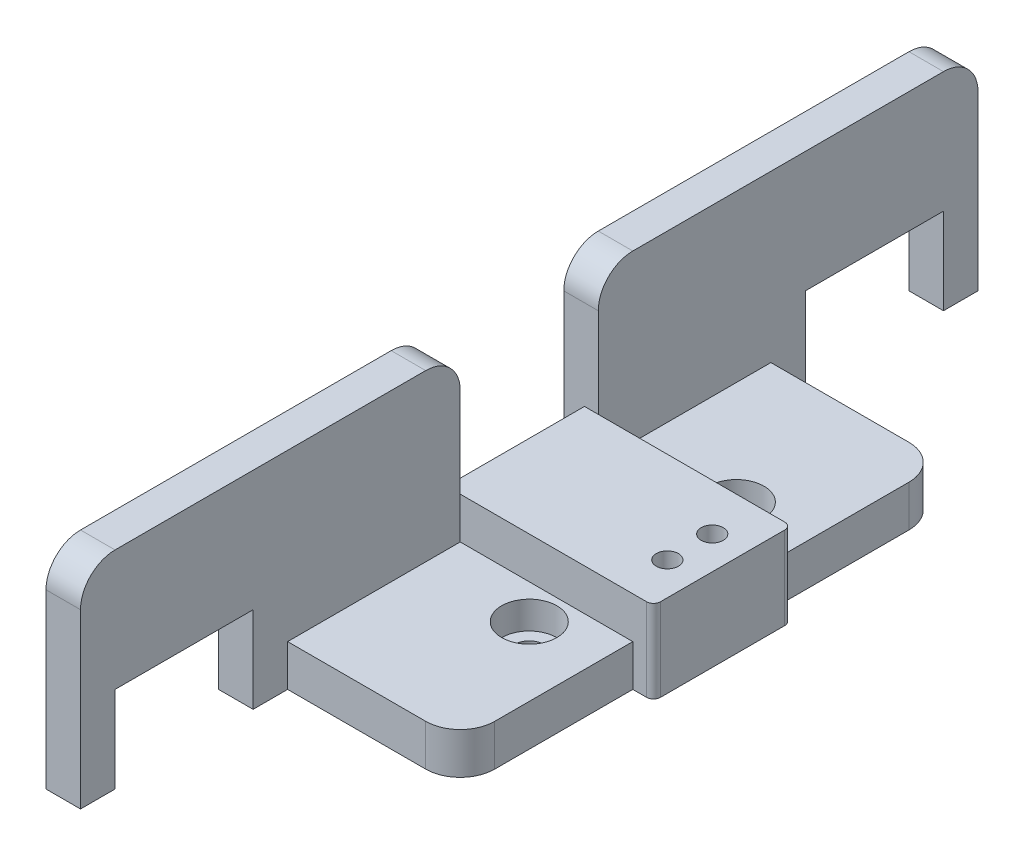
SolidWorks part; units mm, degrees
ref_plane "Front Plane" through (0, 0, 0) normal (0, 0, 1) x (1, 0, 0)
ref_plane "Top Plane" through (0, 0, 0) normal (0, 1, 0) x (1, 0, 0)
ref_plane "Right Plane" through (0, 0, 0) normal (1, 0, 0) x (0, 0, -1)
sketch "Sketch1" plane through (0, 0, 0) normal (0, 1, 0) x (1, 0, 0)
  line L0 (-25, -35) -> (-25, -65)
  line L1 (-25, 35) -> (0, 35)
  line L3 (-25, -35) -> (0, -35)
  line L4 (0, 35) -> (0, -35)
  line L5 (-30, 65) -> (-25, 65)
  line L6 (-30, 65) -> (-30, -65)
  line L7 (-30, -65) -> (-25, -65)
  line L8 (-25, 65) -> (-25, 35)
  point P4 (0, 0)
  point P10 (-30, 0)
  dimension "D1" = 30
  dimension "D2" = 70
  dimension "D3" = 130
  dimension "D4" = 5
extrude "Boss-Extrude1" add sketch "Sketch1" along normal blind 6
sketch "Sketch2" plane through (0, 6, 0) normal (0, 1, 0) x (1, 0, 0)
  line L1 (-30, 65) -> (-25, 65)
  line L2 (-30, 65) -> (-30, -65)
  line L3 (-30, -65) -> (-25, -65)
  line L4 (-25, 65) -> (-25, -65)
extrude "Boss-Extrude2" add sketch "Sketch2" along normal blind 24
sketch "Sketch3" plane through (-30, 0, 0) normal (-1, 0, 0) x (0, 0, 1)
  line L0 (0, 0) -> (0, 30) construction
  line L1 (-65, 30) -> (65, 30) construction
  line L2 (-65, 0) -> (65, 0) construction
  line L3 (-60, 0) -> (-40, 0)
  line L4 (-60, 0) -> (-60, 12.5)
  line L5 (-60, 12.5) -> (-40, 12.5)
  line L6 (-40, 0) -> (-40, 12.5)
  line L7 (60, 12.5) -> (40, 12.5)
  line L8 (40, 0) -> (40, 12.5)
  line L9 (60, 0) -> (40, 0)
  line L10 (60, 0) -> (60, 12.5)
  point P15 (-50, 0)
  point P16 (50, 0)
  dimension "D1" = 100
  dimension "D2" = 20
  dimension "D3" = 12.5
extrude "Cut-Extrude1" cut sketch "Sketch3" against normal through all
sketch "Sketch4" plane through (0, 6, 0) normal (0, 1, 0) x (1, 0, 0)
  line L0 (0, 0) -> (-30, 0) construction
  line L1 (-30, 65) -> (-30, -65) construction
  line L2 (-10, 35) -> (-10, -35) construction
  line L3 (0, 35) -> (-25, 35) construction
  line L4 (-25, -35) -> (0, -35) construction
  line L5 (-25, -35) -> (-25, 35) construction
  line L6 (0, 30) -> (-25, 30) construction
  line L7 (0, 30) -> (0, -30) construction
  line L8 (0, -30) -> (-25, -30) construction
  line L9 (-25, 30) -> (-25, -30) construction
  point P5 (-10, 0)
  point P16 (0, 0)
  point P17 (-10, 15)
  point P18 (-10, -15)
  dimension "D1" = 20
  dimension "D2" = 60
  dimension "D3" = 30
hole_wizard "CBORE for M4 SHCS1" positions "Sketch8" profile "Sketch6" counterbore size "M4" standard "ANSI Metric" end condition through all
sketch "Sketch8" plane through (0, 6, 0) normal (0, 1, 0) x (1, 0, 0)
  point P4 (-10, 15)
  point P7 (-10, -15)
sketch "Sketch6" plane through (-10, 6, -15) normal (1, 0, 0) x (0, 0, 1)
  line L0 (0, 0) -> (0, 6)
  line L1 (0, 6) -> (2.25, 6)
  line L3 (2.25, 6) -> (2.25, 4)
  line L4 (2.25, 4) -> (4, 4)
  line L5 (4, 4) -> (4, 0)
  line L7 (4, 0) -> (0, 0)
  line L11 (0, -6.35) -> (0, 107.95) construction
  dimension "Thru Hole Dia." = 4.5
  dimension "Thru Hole Depth" = 6
  dimension "C'Bore Dia." = 8
  dimension "C'Bore Depth" = 4
sketch "Sketch9" plane through (0, 30, 0) normal (0, 1, 0) x (1, 0, 0)
  line L0 (-30, 65) -> (-30, -65) construction
  line L1 (-30, 10) -> (-25, 10)
  line L2 (-30, 10) -> (-30, -10)
  line L3 (-30, -10) -> (-25, -10)
  line L4 (-25, 10) -> (-25, -10)
  line L5 (-25, 30) -> (-25, -30) construction
  point P8 (-30, 0)
  dimension "D1" = 20
extrude "Cut-Extrude2" cut sketch "Sketch9" against normal blind 18
sketch "Sketch10" plane through (0, 12, 0) normal (0, 1, 0) x (1, 0, 0)
  line L0 (-30, -10) -> (-25, -10) construction
  line L1 (-30, 10) -> (3, 10)
  line L2 (-30, 10) -> (-30, -10)
  line L3 (-30, -10) -> (3, -10)
  line L4 (3, 10) -> (3, -10)
  dimension "D1" = 33
extrude "Boss-Extrude3" add sketch "Sketch10" against normal through all
sketch "Sketch11" plane through (0, 12, 0) normal (0, 1, 0) x (1, 0, 0)
  line L0 (-1.75, 4.5339) -> (-1.75, -4.5339) construction
  line L2 (0, 0) -> (-42.0241, 0) construction
  line L3 (3, -10) -> (3, 10) construction
  circle A0 centre (-1.75, 3.25) radius 1.6
  circle A1 centre (-1.75, -3.25) radius 1.6
  point P2 (-1.75, 0)
  point P8 (-1.75, 3.25)
  point P9 (-1.75, -3.25)
  dimension "D3" = 3.2
  dimension "D1" = 4.75
  dimension "D2" = 6.5
fillet "Fillet1" radius 5 6 edges at (-27.5, 30, -65) (0, 3, -35) (0, 3, 35) (-27.5, 30, 65) (-27.5, 30, -10) (-27.5, 30, 10)
fillet "Fillet2" [suppressed] radius 2
sketch "Sketch13" plane through (-30, 0, 0) normal (-1, 0, 0) x (0, 0, 1)
  line L0 (0, 12) -> (0, 0) construction
  line L1 (-10, 12) -> (10, 12) construction
  line L2 (0, 6) -> (-20, 6) construction
  circle A0 centre (-20, 6) radius 2.5
  circle A1 centre (20, 6) radius 2.5
  point P7 (20, 6)
  point P8 (-20, 6)
  dimension "D2" = 5
  dimension "D1" = 20
extrude "Cut-Extrude3" cut sketch "Sketch13" against normal blind 4.1
chamfer "Chamfer1" distance 3 angle 45 1 edges at (-30, 12, 0)
extrude "Cut-Extrude4" cut sketch "Sketch11" against normal blind 4.5
fillet "Fillet3" radius 1 2 edges at (3, 6, 10) (3, 6, -10)
